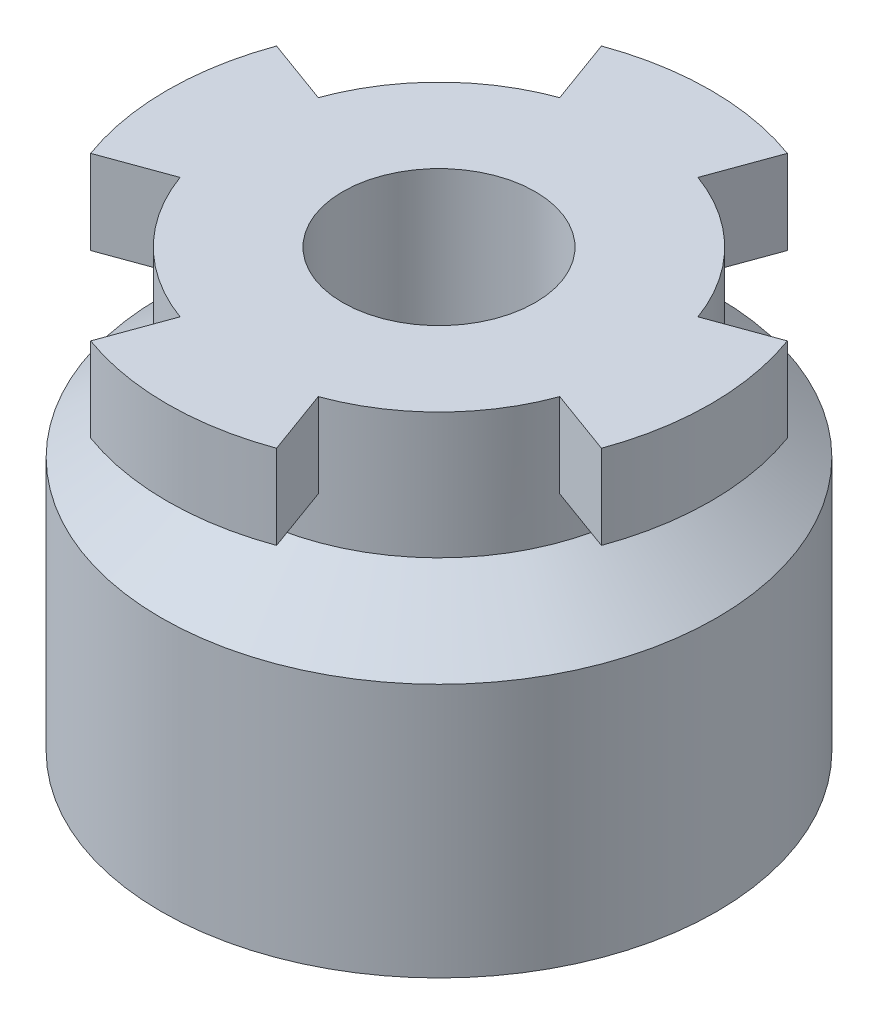
SolidWorks part; units mm, degrees
ref_plane "Płaszczyzna przednia" through (0, 0, 0) normal (0, 0, 1) x (1, 0, 0)
ref_plane "Płaszczyzna górna" through (0, 0, 0) normal (0, 1, 0) x (1, 0, 0)
ref_plane "Płaszczyzna prawa" through (0, 0, 0) normal (1, 0, 0) x (0, 0, -1)
sketch "Szkic1" plane through (0, 0, 0) normal (0, 0, 1) x (1, 0, 0)
  line L0 (0, 0) -> (-23.1, 0)
  line L1 (-23.1, 0) -> (-23.1, 21.15)
  line L2 (-23.1, 21.15) -> (-16.8, 25.8)
  line L3 (-16.8, 25.8) -> (-16.8, 36.3)
  line L4 (-16.8, 36.3) -> (-8, 36.3)
  line L5 (-8, 36.3) -> (-8, 22.3)
  line L6 (-8, 22.3) -> (0, 22.3)
  line L7 (0, 22.3) -> (0, 0)
  dimension "D1" = 36.3
  dimension "D2" = 23.1
  dimension "D3" = 16.8
  dimension "D4" = 10.5
  dimension "D5" = 21.15
  dimension "D6" = 14
  dimension "D7" = 8
revolve "Obrót1" add sketch "Szkic1" angle 360 about L7
sketch "Szkic2" plane through (0, 36.3, 0) normal (0, 1, 0) x (1, 0, 0)
  line L0 (0, 0) -> (-7.7297, 21.2371)
  line L1 (0, 0) -> (7.7297, 21.2371)
  line L2 (0, 0) -> (0, 27.471) construction
  line L3 (15.7868, -5.7459) -> (21.2371, -7.7297)
  line L4 (15.7868, 5.7459) -> (21.2371, 7.7297)
  line L5 (-5.7459, -15.7868) -> (-7.7297, -21.2371)
  line L6 (5.7459, -15.7868) -> (7.7297, -21.2371)
  line L7 (-15.7868, 5.7459) -> (-21.2371, 7.7297)
  line L8 (-15.7868, -5.7459) -> (-21.2371, -7.7297)
  arc A0 (-7.7297, 21.2371) -> (7.7297, 21.2371) centre (0, 0) cw
  arc A1 (5.7459, 15.7868) -> (-5.7459, 15.7868) centre (0, 0) ccw
  circle A2 centre (0, 0) radius 16.8 construction
  arc A3 (15.7868, -5.7459) -> (15.7868, 5.7459) centre (0, 0) ccw
  arc A4 (21.2371, 7.7297) -> (21.2371, -7.7297) centre (0, 0) cw
  arc A5 (-5.7459, -15.7868) -> (5.7459, -15.7868) centre (0, 0) ccw
  arc A6 (7.7297, -21.2371) -> (-7.7297, -21.2371) centre (0, 0) cw
  arc A7 (-15.7868, 5.7459) -> (-15.7868, -5.7459) centre (0, 0) ccw
  arc A8 (-21.2371, -7.7297) -> (-21.2371, 7.7297) centre (0, 0) cw
  point P28 (0, 0)
  circle M4 centre (0, 0) radius 16.8
  dimension "D1" = 22.6
  dimension "D2" = 22.6
  dimension "D3" = 40
  dimension "D4" = 20
  dimension "D5" = 4
extrude "Dodanie-wyciągnięcie1" add sketch "Szkic2" against normal blind 7 contours L2 L1 A0 M4 | A1 L2 A0 L0 | L7 A8 L8 A7 | L5 A6 L6 A5 | L3 A4 L4 A3
sketch "Szkic3" plane through (0, 36.3, 0) normal (0, 1, 0) x (1, 0, 0)
  line L0 (0, 0) -> (11.8794, 11.8794)
  arc A0 (15.7868, 5.7459) -> (5.7459, 15.7868) centre (0, 0) ccw construction
